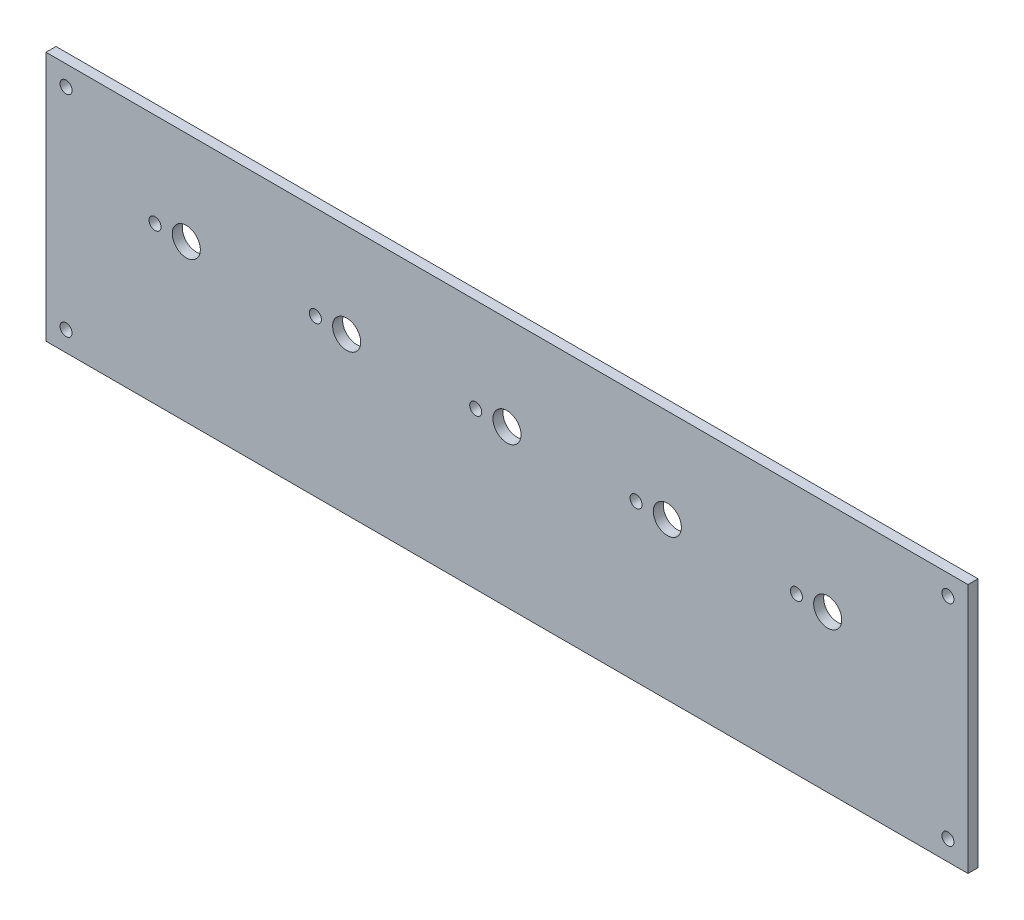
SolidWorks part; units mm, degrees
ref_plane "Front Plane" through (0, 0, 0) normal (0, 0, 1) x (1, 0, 0)
ref_plane "Top Plane" through (0, 0, 0) normal (0, 1, 0) x (1, 0, 0)
ref_plane "Right Plane" through (0, 0, 0) normal (1, 0, 0) x (0, 0, -1)
sketch "Sketch1" plane through (0, 0, 0) normal (0, 0, 1) x (1, 0, 0)
  line L1 (0, 0) -> (230, 0)
  line L2 (0, 0) -> (0, 62.43)
  line L3 (0, 62.43) -> (230, 62.43)
  line L4 (230, 0) -> (230, 62.43)
  dimension "D1" = 62.43
  dimension "D2" = 230
extrude "Boss-Extrude1" add sketch "Sketch1" along normal blind 2.5
sketch "Sketch2" plane through (0, 0, 2.5) normal (0, 0, 1) x (1, 0, 0)
  line L1 (230, 62.43) -> (0, 62.43) construction
  line L2 (0, 62.43) -> (0, 0) construction
  line L3 (115, 0) -> (115, 62.43) construction
  line L4 (0, 0) -> (230, 0) construction
  line L5 (0, 31.215) -> (230, 31.215) construction
  line L6 (230, 0) -> (230, 62.43) construction
  circle A0 centre (5, 57.43) radius 1.5
  circle A1 centre (5, 5) radius 1.5
  circle A2 centre (225, 5) radius 1.5
  circle A3 centre (225, 57.43) radius 1.5
  dimension "D1" = 3
  dimension "D2" = 5
  dimension "D3" = 5
extrude "Cut-Extrude1" cut sketch "Sketch2" against normal blind 10
sketch "Sketch3" plane through (0, 0, 2.5) normal (0, 0, 1) x (1, 0, 0)
  line L0 (0, 31.215) -> (230, 31.215) construction
  line L1 (0, 62.43) -> (0, 0) construction
  line L2 (230, 0) -> (230, 62.43) construction
  line L3 (115, 62.43) -> (115, 0) construction
  line L4 (230, 62.43) -> (0, 62.43) construction
  line L5 (0, 0) -> (230, 0) construction
  line L6 (0, 62.43) -> (115, 31.215) construction
  line L7 (115, 62.43) -> (0, 31.215) construction
  line L8 (57.5, 46.8225) -> (230, 46.8225) construction
  line L9 (57.5, 46.8225) -> (0, 46.8225) construction
  line L10 (0, 46.8225) -> (115, 31.215) construction
  line L11 (0, 31.215) -> (115, 46.8225) construction
  line L12 (57.5, 39.0187) -> (230, 39.0187) construction
  line L13 (57.5, 39.0187) -> (0, 39.0187) construction
  line L14 (57.5, 39.0187) -> (57.5, 31.215) construction
  line L15 (57.5, 39.0187) -> (57.5, 62.43) construction
  circle A0 centre (115, 39.0187) radius 3.5
  circle A1 centre (107.2, 39.0187) radius 1.5
  circle A2 centre (155, 39.0187) radius 3.5
  circle A3 centre (147.2, 39.0187) radius 1.5
  circle A4 centre (195, 39.0187) radius 3.5
  circle A5 centre (187.2, 39.0187) radius 1.5
  circle A6 centre (67.2, 39.0187) radius 1.5
  circle A7 centre (75, 39.0187) radius 3.5
  circle A8 centre (27.2, 39.0187) radius 1.5
  circle A9 centre (35, 39.0187) radius 3.5
  dimension "D1" = 7
  dimension "D2" = 3
  dimension "D3" = 7.8
  dimension "D4" = 3
  dimension "D5" = 3
extrude "Cut-Extrude2" cut sketch "Sketch3" against normal up to surface (2.5 mm away) up to face at (223.5, 57.43, 0)
